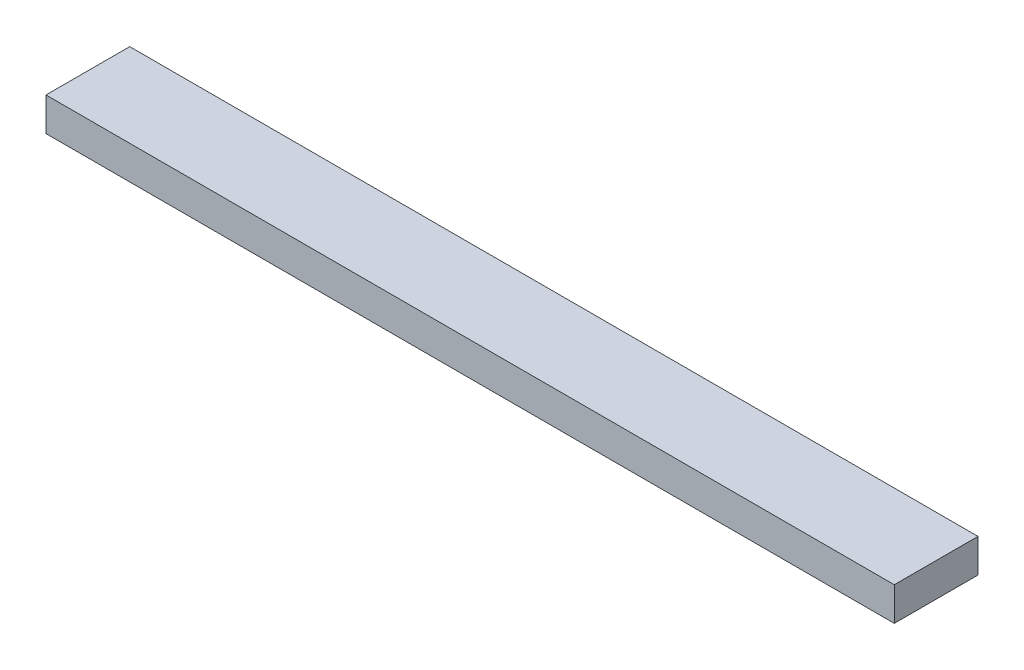
SolidWorks part; units mm, degrees
ref_plane "前视基准面" through (0, 0, 0) normal (0, 0, 1) x (1, 0, 0)
ref_plane "上视基准面" through (0, 0, 0) normal (0, 1, 0) x (1, 0, 0)
ref_plane "右视基准面" through (0, 0, 0) normal (1, 0, 0) x (0, 0, -1)
sketch "草图1" plane through (0, 0, 0) normal (0, 0, 1) x (1, 0, 0)
  line L1 (-152, 26.0571) -> (152, 26.0571)
  line L2 (-152, 26.0571) -> (-152, 14.0571)
  line L3 (-152, 14.0571) -> (152, 14.0571)
  line L4 (152, 26.0571) -> (152, 14.0571)
  dimension "D1" = 304
  dimension "D2" = 12
  dimension "D3" = 152
extrude "凸台-拉伸1" add sketch "草图1" along normal blind 30
